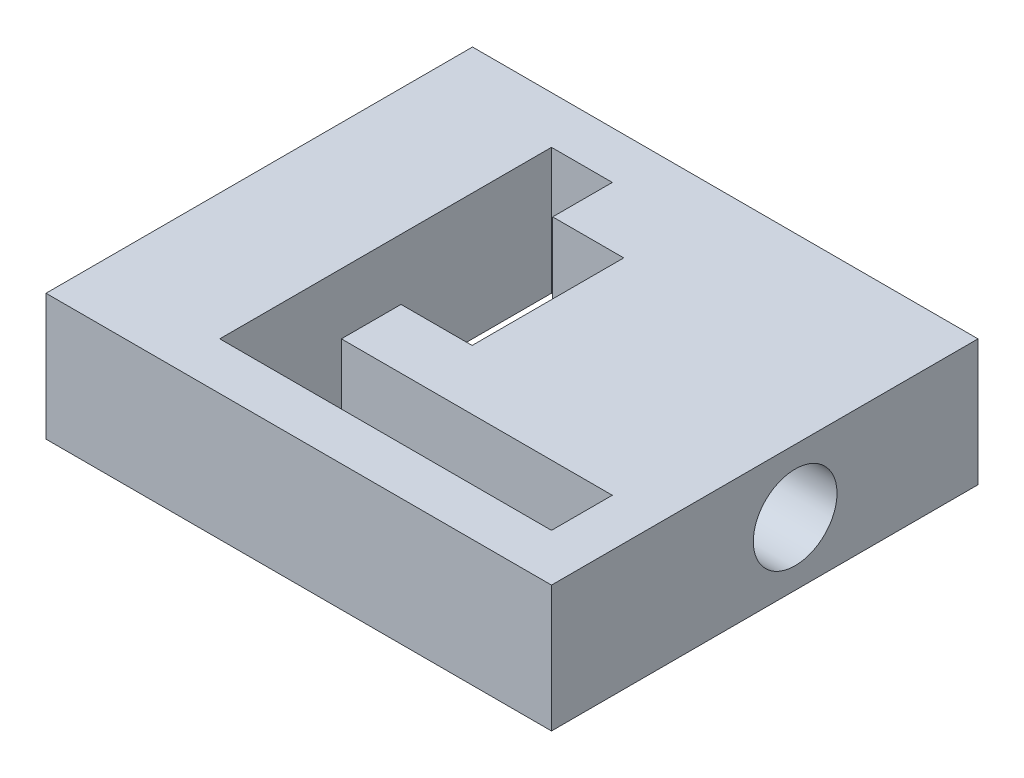
SolidWorks part; units mm, degrees
ref_plane "Front Plane" through (0, 0, 0) normal (0, 0, 1) x (1, 0, 0)
ref_plane "Top Plane" through (0, 0, 0) normal (0, 1, 0) x (1, 0, 0)
ref_plane "Right Plane" through (0, 0, 0) normal (1, 0, 0) x (0, 0, -1)
sketch "Sketch1" plane through (0, 0, 0) normal (0, 1, 0) x (1, 0, 0)
  line L0 (3, 24) -> (3, 3)
  line L1 (0, 0) -> (27, 0)
  line L2 (0, 0) -> (0, 27)
  line L3 (0, 27) -> (27, 27)
  line L4 (27, 0) -> (27, 27)
  line L5 (3, 3) -> (24, 3)
  line L6 (24, 3) -> (24, 6.85)
  line L7 (24, 6.85) -> (6.85, 6.85)
  line L8 (6.85, 6.85) -> (6.85, 24)
  line L9 (6.85, 24) -> (3, 24)
  line L10 (3, 3) -> (0, 3) construction
  line L11 (24, 3) -> (27, 3) construction
  point P14 (0, 13.5)
  point P15 (3, 13.5)
  dimension "D1" = 21
  dimension "D2" = 3.85
  dimension "D3" = 3
  dimension "D4" = 3
extrude "Boss-Extrude1" add sketch "Sketch1" along normal blind 8
sketch "Sketch2" plane through (0, 8, 0) normal (0, 1, 0) x (1, 0, 0)
  line L0 (6.85, 6.85) -> (6.85, 24) construction
  line L1 (6.85, 20.225) -> (11.35, 20.225)
  line L2 (6.85, 20.225) -> (6.85, 10.625)
  line L3 (6.85, 10.625) -> (11.35, 10.625)
  line L4 (11.35, 20.225) -> (11.35, 10.625)
  point P7 (6.85, 15.425)
  point P8 (6.85, 15.425)
  dimension "D1" = 9.6
  dimension "D2" = 4.5
extrude "Cut-Extrude1" cut sketch "Sketch2" against normal through all
sketch "Sketch3" plane through (27, 0, 0) normal (1, 0, 0) x (0, 0, -1)
  line L0 (10.625, 4) -> (20.225, 4) construction
  line L4 (20.225, 8) -> (10.625, 8)
  line L5 (20.225, 0) -> (20.225, 8)
  line L6 (10.625, 0) -> (20.225, 0)
  line L7 (10.625, 8) -> (10.625, 0)
  line L8 (20.225, 8) -> (10.625, 8) construction
  line L9 (20.225, 0) -> (20.225, 8) construction
  line L10 (10.625, 0) -> (20.225, 0) construction
  line L11 (10.625, 8) -> (10.625, 0) construction
  circle A0 centre (15.425, 4) radius 2.65
  dimension "D2" = 5.3
  dimension "D1" = 0
extrude "Cut-Extrude2" cut sketch "Sketch3" against normal up to surface (15.65 mm away) up to face at (11.35, 4, -15.425)
sketch "Sketch4" plane through (0, 0, 0) normal (-1, 0, 0) x (0, 0, 1)
  line L0 (-22.78, 5) -> (-13.5, 5) construction
  line L1 (-27, 0) -> (0, 0)
  line L2 (-27, 0) -> (-27, 8)
  line L3 (-27, 8) -> (0, 8)
  line L4 (0, 0) -> (0, 8)
  line L5 (-13.5, 5) -> (-4.22, 5) construction
  line L6 (-13.5, 8) -> (-13.5, 5) construction
  line L7 (-27, 8) -> (0, 8) construction
  circle A0 centre (-22.78, 5) radius 1.25
  circle A1 centre (-4.22, 5) radius 1.25
  dimension "D2" = 2.5
  dimension "D1" = 18.56
  dimension "D3" = 3
extrude "Boss-Extrude2" add sketch "Sketch4" along normal blind 5
equation "\"8mm hole\" = 8.4mm'used to be the diameter of the linear motion rods"
equation "\"22mm hole\"= 23mm'this is the size of the hole for the nema 17 standard was 22mm"
equation "\"15mm hole\"= 15.8mm'this is the hole for the linear motion sliders, they are all set to this measurement so if you have different sized bearing sliders you may have to adjust individually"
equation "\"bed height offset\"= 3mm'this is how far the bed has been offset from a low point (probably don't want to edit, but can)"
equation "\"#10 nut width\"= 9.6mm'this is the width of a nut from flat side to other flat side"
equation "\"#10 bolt diameter\"= 5mm'This is the diameter including the threads"
equation "\"Al_width\"= 19.31mm'Self explainatory"
equation "\"Al_thick\"= 3.35mm"
equation "\"lin_rd_vert_hole_tol\"= 0.5mm"
equation "\"lin_rd_horz_hole_tol\"= 0.5mm"
equation "\"lin_rd_diam\"= 8mm"
equation "\"slid_diam\"= 15mm"
equation "\"slid_vert_tol\"= 0.7mm"
equation "\"mot_face_ridge_diam\"= 22mm"
equation "\"mot_face_ridge_tol\"= 1mm"
equation "\"slid_horz_tol\"= 0.8"
equation "\"Al_thick_tol\" = 0.45mm"
equation "\"Al_width_tol\" = 0.7mm"
equation "\"D2@Sketch1\"=\"Al_thick\" + \"Al_thick_tol\" + 0.05"
equation "\"D1@Sketch2\"= \"#10 nut width\""
